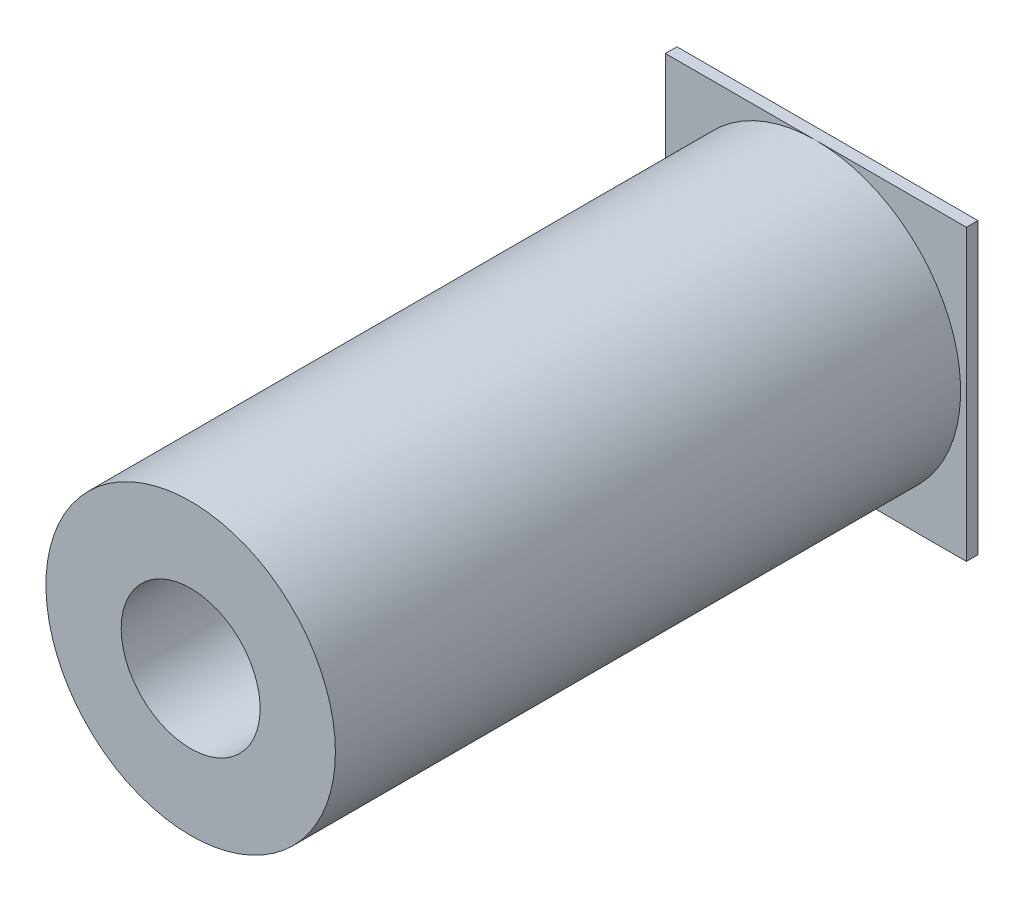
SolidWorks part; units mm, degrees
ref_plane "Front Plane" through (0, 0, 0) normal (0, 0, 1) x (1, 0, 0)
ref_plane "Top Plane" through (0, 0, 0) normal (0, 1, 0) x (1, 0, 0)
ref_plane "Right Plane" through (0, 0, 0) normal (1, 0, 0) x (0, 0, -1)
sketch "Sketch1" plane through (0, 0, 0) normal (0, 0, 1) x (1, 0, 0)
  line L1 (-13, 12.5) -> (13, 12.5)
  line L2 (-13, 12.5) -> (-13, -12.5)
  line L3 (-13, -12.5) -> (13, -12.5)
  line L4 (13, 12.5) -> (13, -12.5)
  line L5 (-13, 12.5) -> (13, -12.5) construction
  line L6 (-13, -12.5) -> (13, 12.5) construction
  point P0 (0, 0)
  dimension "D1" = 26
  dimension "D2" = 25
extrude "Boss-Extrude1" add sketch "Sketch1" along normal blind 1
sketch "Sketch2" plane through (0, 0, 1) normal (0, 0, 1) x (1, 0, 0)
  circle A0 centre (0, 0) radius 12.5
extrude "Boss-Extrude2" add sketch "Sketch2" along normal blind 54
sketch "Sketch3" plane through (0, 0, 0) normal (0, 0, -1) x (-1, 0, 0)
  circle A0 centre (0, 0) radius 6
  dimension "D1" = 12
extrude "Cut-Extrude1" cut sketch "Sketch3" against normal through all
